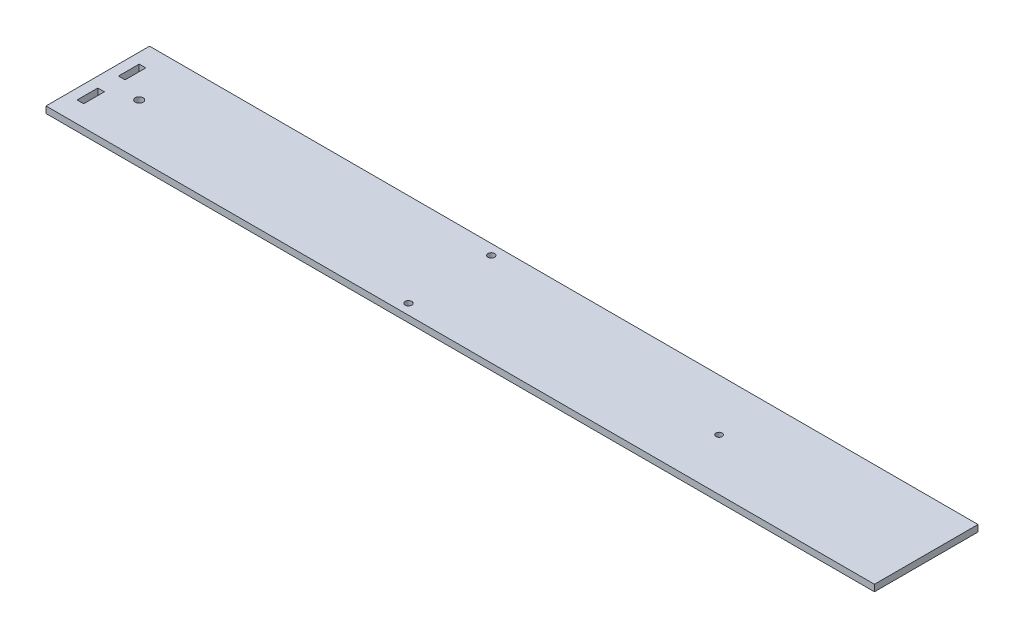
SolidWorks part; units mm, degrees
ref_plane "Front Plane" through (0, 0, 0) normal (0, 0, 1) x (1, 0, 0)
ref_plane "Top Plane" through (0, 0, 0) normal (0, 1, 0) x (1, 0, 0)
ref_plane "Right Plane" through (0, 0, 0) normal (1, 0, 0) x (0, 0, -1)
sketch "Sketch1" plane through (0, 0, 0) normal (0, 1, 0) x (1, 0, 0)
  line L0 (0, 50) -> (0, 40) construction
  line L1 (0, 0) -> (400, 0)
  line L2 (0, 0) -> (0, 50)
  line L3 (0, 50) -> (400, 50)
  line L4 (400, 0) -> (400, 50)
  line L5 (200, 50) -> (200, 0) construction
  line L6 (0, 25) -> (400, 25) construction
  line L7 (0, 40) -> (5, 40) construction
  line L8 (5, 40) -> (5, 30) construction
  line L9 (5, 30) -> (5, 20) construction
  line L10 (5, 20) -> (5, 10) construction
  line L11 (5, 10) -> (8.175, 10)
  line L12 (8.175, 10) -> (8.175, 20)
  line L13 (8.175, 20) -> (5, 20)
  line L14 (5, 20) -> (5, 10)
  line L15 (5, 30) -> (8.175, 30)
  line L16 (8.175, 30) -> (8.175, 40)
  line L17 (8.175, 40) -> (5, 40)
  line L18 (5, 40) -> (5, 30)
  line L19 (5, 40) -> (5, 30) construction
  line L20 (400, 25) -> (300, 25) construction
  line L21 (400, 25) -> (170, 25) construction
  line L22 (170, 25) -> (170, 45) construction
  line L23 (0, 25) -> (20, 25) construction
  circle A0 centre (300, 25) radius 1.5
  circle A1 centre (170, 45) radius 1.6
  circle A2 centre (170, 5) radius 1.6
  circle A3 centre (20, 25) radius 1.9
  point P28 (200, 25)
  dimension "D4" = 3
  dimension "D5" = 3.2
  dimension "D12" = 3.8
  dimension "D1" = 50
  dimension "D2" = 400
  dimension "D3" = 2
  dimension "D7" = 10
  dimension "D8" = 3.175
  dimension "D9" = 230
  dimension "D10" = 100
  dimension "D11" = 5
  dimension "D6" = 2
extrude "Boss-Extrude1" add sketch "Sketch1" along normal blind 3.175
